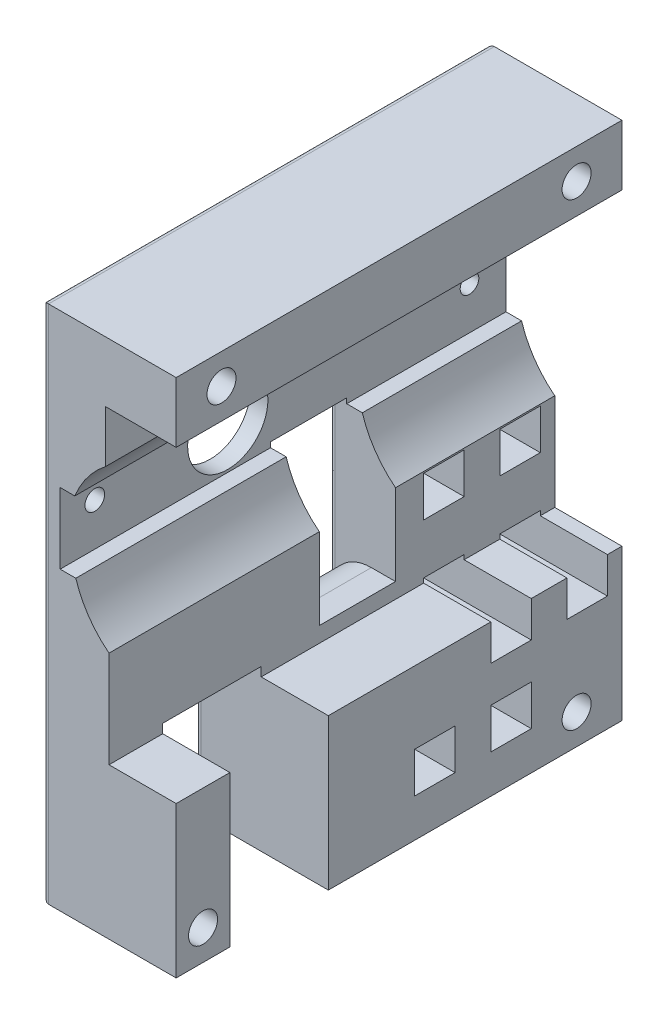
SolidWorks part; units mm, degrees
ref_plane "Front" through (0, 0, 0) normal (0, 0, 1) x (1, 0, 0)
ref_plane "Top" through (0, 0, 0) normal (0, 1, 0) x (1, 0, 0)
ref_plane "Right" through (0, 0, 0) normal (1, 0, 0) x (0, 0, -1)
sketch "Profile" plane through (0, 0, 0) normal (0, 0, 1) x (1, 0, 0)
  line L0 (10.2613, -54.1947) -> (10.2613, -29.1947)
  line L1 (-11.8487, -54.1947) -> (10.2613, -54.1947)
  line L2 (-11.8487, -54.1947) -> (-11.8487, 31.8453)
  line L3 (-11.8487, 31.8453) -> (10.2613, 31.8453)
  line L4 (10.2613, 21.8453) -> (10.2613, 31.8453)
  line L7 (10.2613, -29.1947) -> (-0.8487, -29.1947)
  line L8 (-0.8487, -29.1947) -> (-0.8487, -13.1947)
  line L10 (10.2613, 21.8453) -> (-1.3887, 21.8453)
  line L11 (-1.3887, 21.8453) -> (-1.3887, 13.2835)
  line L12 (-6.5097, 6.4953) -> (-8.9287, 6.4953)
  line L13 (-8.9287, 6.4953) -> (-8.9287, -5.2047)
  line L14 (-8.9287, -5.2047) -> (-6.3407, -5.2047)
  arc A0 (-6.3407, -5.2047) -> (-0.8487, -13.1947) centre (9.1965, -0.4075) ccw
  arc A1 (-6.5097, 6.4953) -> (-1.3887, 13.2835) centre (8.5807, 0.4371) cw
  point P0 (0, 0)
  dimension "D15" = 16.261
  dimension "D16" = 16.261
  dimension "D1" = 86.04
  dimension "D2" = 22.11
  dimension "D3" = 10
  dimension "D4" = 25
  dimension "D5" = 22.11
  dimension "D6" = 11.11
  dimension "D7" = 11.65
  dimension "D8" = 8.5617
  dimension "D9" = 16
  dimension "D10" = 2.588
  dimension "D11" = 11.7
  dimension "D12" = 2.4191
  dimension "D13" = 5.492
  dimension "D14" = 23.99
extrude "ProfileExtrude" add sketch "Profile" along normal blind 73.76
sketch "HoseWindow" plane through (-11.8487, 0, 0) normal (-1, 0, 0) x (0, 0, 1)
  line L0 (73.76, -54.1947) -> (0, -54.1947) construction
  line L1 (64.87, -54.1947) -> (48.58, -54.1947)
  line L2 (64.87, -54.1947) -> (64.87, -27.6947)
  line L3 (64.87, -27.6947) -> (48.58, -27.6947)
  line L4 (48.58, -54.1947) -> (48.58, -27.6947)
  dimension "D1" = 16.29
  dimension "D2" = 26.5
  dimension "D3" = 8.89
extrude "HoseWindowCut" cut sketch "HoseWindow" against normal through all
sketch "CageScrews" plane through (-11.8487, 0, 0) normal (-1, 0, 0) x (0, 0, 1)
  line L0 (73.76, 31.8453) -> (0, 31.8453) construction
  line L1 (0, 31.8453) -> (0, -54.1947) construction
  line L2 (73.76, 31.8453) -> (73.76, -54.1947) construction
  line L3 (73.76, -54.1947) -> (64.87, -54.1947) construction
  line L4 (48.58, -54.1947) -> (0, -54.1947) construction
  circle A0 centre (7.5, 26.8453) radius 2.4
  circle A1 centre (66.26, 26.8453) radius 2.4
  circle A2 centre (7.5, -49.1947) radius 2.4
  circle A3 centre (69.31, -49.1947) radius 2.4
  dimension "D1" = 4.8
  dimension "D2" = 5
  dimension "D3" = 7.5
  dimension "D4" = 7.5
  dimension "D5" = 5
  dimension "D6" = 5
  dimension "D7" = 4.45
  dimension "D8" = 5
  dimension "D9" = 7.5
extrude "CageScrewsCut" cut sketch "CageScrews" against normal through all
sketch "AxleHole" plane through (-11.8487, 0, 0) normal (-1, 0, 0) x (0, 0, 1)
  line L0 (46.03, -4.7837) -> (46.03, 6.7405) construction
  line L1 (47.361, 8.3595) -> (47.361, 6.7405)
  line L2 (47.361, 6.7405) -> (44.699, 6.7405)
  line L3 (44.699, 6.7405) -> (44.699, 8.3595)
  line L5 (48.58, -54.1947) -> (0, -54.1947) construction
  line L6 (0, 31.8453) -> (0, -54.1947) construction
  line L7 (39.391, 1.8553) -> (52.669, 1.8553) construction
  arc A0 (44.699, 8.3595) -> (47.361, 8.3595) centre (46.03, 1.8553) ccw
  dimension "D1" = 13.278
  dimension "D2" = 1.331
  dimension "D3" = 1.619
  dimension "D4" = 1.619
  dimension "D5" = 46.03
  dimension "D6" = 56.05
extrude "AxleHoleCut" cut sketch "AxleHole" against normal through all
sketch "SetScrewHoles" plane through (-11.8487, 0, 0) normal (-1, 0, 0) x (0, 0, 1)
  line L0 (47.361, 6.7405) -> (44.699, 6.7405) construction
  circle A0 centre (6.03, 1.8553) radius 1.5394
  circle A1 centre (68.03, 1.8553) radius 1.629
  point P6 (46.03, 6.7405)
  point P7 (46.03, 6.7405)
  dimension "D1" = 22
  dimension "D2" = 40
extrude "SetScrewHolesCut" cut sketch "SetScrewHoles" against normal through all
sketch "VelocityWindow" plane through (-11.8487, 0, 0) normal (-1, 0, 0) x (0, 0, 1)
  line L0 (73.76, 31.8453) -> (73.76, -54.1947) construction
  line L1 (38.96, -26.6447) -> (26.35, -26.6447)
  line L2 (38.96, -26.6447) -> (38.96, -4.3547)
  line L3 (38.96, -4.3547) -> (26.35, -4.3547)
  line L4 (26.35, -26.6447) -> (26.35, -4.3547)
  line L5 (38.96, -26.6447) -> (26.35, -4.3547) construction
  line L6 (38.96, -4.3547) -> (26.35, -26.6447) construction
  line L7 (48.58, -54.1947) -> (0, -54.1947) construction
  point P0 (32.655, -15.4997)
  dimension "D1" = 12.61
  dimension "D2" = 22.29
  dimension "D3" = 34.8
  dimension "D4" = 27.55
extrude "VelocityWindowCut" cut sketch "VelocityWindow" against normal through all
fillet "Fillet3" radius 7 1 edges at (-11.8487, -26.6447, 32.655)
sketch "TriggerRackSlotCut" plane through (-11.8487, 0, 0) normal (-1, 0, 0) x (0, 0, 1)
  line L0 (15, -41.1447) -> (21.7, -41.1447)
  line L1 (15, -41.1447) -> (15, -47.8447)
  line L2 (21.7, -41.1447) -> (21.7, -47.8447)
  line L3 (15, -47.8447) -> (21.7, -47.8447)
  line L4 (0, 31.8453) -> (0, -54.1947) construction
  line L5 (27.6, -41.1447) -> (34.3, -41.1447)
  line L6 (27.6, -41.1447) -> (27.6, -47.8447)
  line L7 (34.3, -41.1447) -> (34.3, -47.8447)
  line L8 (27.6, -47.8447) -> (34.3, -47.8447)
  line L9 (2.4, -28.4447) -> (9.1, -28.4447)
  line L10 (2.4, -28.4447) -> (2.4, -35.1447)
  line L11 (9.1, -28.4447) -> (9.1, -35.1447)
  line L12 (2.4, -35.1447) -> (9.1, -35.1447)
  line L13 (15, -28.4447) -> (21.7, -28.4447)
  line L14 (15, -28.4447) -> (15, -35.1447)
  line L15 (21.7, -28.4447) -> (21.7, -35.1447)
  line L16 (48.58, -54.1947) -> (0, -54.1947) construction
  line L17 (15, -35.1447) -> (21.7, -35.1447)
  line L18 (15, -41.1447) -> (27.6, -41.1447) construction
  line L19 (15, -41.1447) -> (15, -28.4447) construction
  line L20 (2.4, -13.4447) -> (9.1, -13.4447)
  line L21 (2.4, -13.4447) -> (2.4, -20.1447)
  line L22 (9.1, -13.4447) -> (9.1, -20.1447)
  line L23 (2.4, -20.1447) -> (9.1, -20.1447)
  line L24 (15, -13.4447) -> (21.7, -13.4447)
  line L25 (15, -13.4447) -> (15, -20.1447)
  line L26 (21.7, -13.4447) -> (21.7, -20.1447)
  line L27 (15, -20.1447) -> (21.7, -20.1447)
  line L28 (15, -28.4447) -> (2.4, -28.4447) construction
  line L43 (27.6, -28.4447) -> (34.3, -28.4447) [skipped]
  line L44 (27.6, -28.4447) -> (27.6, -35.1447) [skipped]
  line L45 (34.3, -28.4447) -> (34.3, -35.1447) [skipped]
  line L46 (27.6, -35.1447) -> (34.3, -35.1447) [skipped]
  dimension "D1" = 6.35
  dimension "D2" = 15
  dimension "D3" = 6.7
  dimension "D4" = 6.7
  dimension "D7" = 2
  dimension "D5" = 12.6
  dimension "D6" = 12.7
  dimension "D9" = 12.6
  dimension "D8" = 2
extrude "RackSlotCut" cut sketch "TriggerRackSlotCut" against normal through all
fillet "Fillet4" radius 1 35 edges at (-11.8487, -31.7947, 21.7) (-11.8487, -28.4447, 18.35) (-11.8487, -31.7947, 15) (-11.8487, -35.1447, 18.35) (-11.8487, -47.8447, 18.35) (-11.8487, -44.4947, 15) (-11.8487, -41.1447, 18.35) (-11.8487, -44.4947, 21.7) (-11.8487, -47.8447, 30.95) (-11.8487, -44.4947, 34.3) (-11.8487, -18.9997, 38.96) (-11.8487, -4.3547, 32.655) (-11.8487, -18.9997, 26.35) (-11.8487, -11.1747, 0) (-11.8487, -54.1947, 24.29) (-11.8487, -40.9447, 48.58) (-11.8487, -27.6947, 56.725) (-11.8487, -40.9447, 64.87) (-11.8487, -54.1947, 69.315) (-11.8487, -11.1747, 73.76) (-11.8487, 31.8453, 36.88) (-11.8487, -44.4947, 27.6) (-11.8487, -41.1447, 30.95) (-11.8487, -35.1447, 5.75) (-11.8487, -31.7947, 2.4) (-11.8487, -31.7947, 9.1) (-11.8487, -28.4447, 5.75) (-11.8487, -13.4447, 18.35) (-11.8487, -16.7947, 21.7) (-11.8487, -20.1447, 18.35) (-11.8487, -16.7947, 15) (-11.8487, -16.7947, 2.4) (-11.8487, -20.1447, 5.75) (-11.8487, -16.7947, 9.1) (-11.8487, -13.4447, 5.75)
equation "\"CageLeftBottomEdge\"=22.11mm"
equation "\"CageLeftTopEdge\"=22.11mm"
equation "\"CageHeight\"=86.04mm"
equation "\"CageLength\"=73.76mm"
equation "\"CageTopScrewClearance\"=10mm"
equation "\"CageLeftTopDepth\"= 11.65mm"
equation "\"CageLeftBottomDepth\"=11.11mm"
equation "\"CageLeftTopHeight\"=8.56175mm"
equation "\"CageLeftBottomHeight\"=16mm"
equation "\"CageLeftTopChannelDepth\"=2.41908mm"
equation "\"CageLeftBottomChannelDepth\"=2.588mm"
equation "\"CageLeftChannelHeight\"=11.7mm"
equation "\"CageChanRelHeight\"=23.99mm"
equation "\"CageChanRelDepth\"=5.492mm"
equation "\"CageChamberRadius\"=16.261mm"
equation "\"CageScrewDiameter\"=4.8mm"
equation "\"CageSetScrewDiameter\"=3.5mm"
equation "\"CageAxleRadius\"=6.639mm"
equation "\"CageAxleKeyHeight\"=1.619mm"
equation "\"CageAxleKeyWidth\"=2.662mm"
equation "\"CageHoseWindowWidth\"=16.29mm"
equation "\"CageHoseWindowHeight\"=26.5mm"
equation "\"CageHoseWindow-Edge\"=8.89mm"
equation "\"CageScrew-VerticalEdge\"=5.0mm"
equation "\"CageScrew-HorizontalEdge\"=7.5mm"
equation "\"CageScrew-HoseCornerScrewEdge\"=4.45mm"
equation "\"CageAxle-BottomEdge\"=56.05mm"
equation "\"CageBackSetScrew-Axle\"=40mm"
equation "\"CageFrontSetScrew-Axle\"=22mm"
equation "\"CageVelocityWindow-BackEdge\"=34.8mm"
equation "\"CageVelocityWindow-BottomEdge\"=27.55mm"
equation "\"CageVelocityWindowHeight\"=22.29mm"
equation "\"CageVelocityWindowWidth\"=12.61mm"
equation "\"D11@Profile\" = \"CageLeftChannelHeight\""
equation "\"D10@Profile\" = \"CageLeftBottomChannelDepth\""
equation "\"D12@Profile\" = \"CageLeftTopChannelDepth\""
equation "\"D8@Profile\" = \"CageLeftTopHeight\""
equation "\"D9@Profile\" = \"CageLeftBottomHeight\""
equation "\"D6@Profile\" = \"CageLeftBottomDepth\""
equation "\"D7@Profile\" = \"CageLeftTopDepth\""
equation "\"D3@Profile\" = \"CageTopScrewClearance\""
equation "\"CageBottomScrewClearance\"=25mm"
equation "\"D4@Profile\" = \"CageBottomScrewClearance\""
equation "\"D5@Profile\" = \"CageLeftBottomEdge\""
equation "\"D2@Profile\" = \"CageLeftTopEdge\""
equation "\"D1@Profile\" = \"CageHeight\""
equation "\"D13@Profile\" = \"CageChanRelDepth\""
equation "\"D14@Profile\" = \"CageChanRelHeight\""
equation "\"D15@Profile\" = \"CageChamberRadius\""
equation "\"D16@Profile\" = \"CageChamberRadius\""
equation "\"D1@ProfileExtrude\"= \"CageLength\""
equation "\"D3@HoseWindow\" = \"CageHoseWindow-Edge\""
equation "\"D2@HoseWindow\" = \"CageHoseWindowHeight\""
equation "\"D1@HoseWindow\" = \"CageHoseWindowWidth\""
equation "\"D1@CageScrews\"= \"CageScrewDiameter\""
equation "\"D9@CageScrews\" = \"CageScrew-HorizontalEdge\""
equation "\"D7@CageScrews\" = \"CageScrew-HoseCornerScrewEdge\""
equation "\"D4@CageScrews\" = \"CageScrew-HorizontalEdge\""
equation "\"D6@CageScrews\"= \"CageScrew-VerticalEdge\""
equation "\"D5@CageScrews\"= \"CageScrew-VerticalEdge\""
equation "\"D8@CageScrews\"= \"CageScrew-VerticalEdge\""
equation "\"D2@CageScrews\"= \"CageScrew-VerticalEdge\""
equation "\"D1@AxleHole\" = \"CageAxleRadius\" * 2"
equation "\"D4@AxleHole\" = \"CageAxleKeyHeight\""
equation "\"D3@AxleHole\" = \"CageAxleKeyHeight\""
equation "\"D2@AxleHole\" = \"CageAxleKeyWidth\" / 2"
equation "\"CageAxle-FrontEdge\"=46.03mm"
equation "\"D6@AxleHole\" = \"CageAxle-BottomEdge\""
equation "\"D5@AxleHole\" = \"CageAxle-FrontEdge\""
equation "\"D2@SetScrewHoles\" = \"CageBackSetScrew-Axle\""
equation "\"D1@SetScrewHoles\" = \"CageFrontSetScrew-Axle\""
equation "\"D1@VelocityWindow\" = \"CageVelocityWindowWidth\""
equation "\"D2@VelocityWindow\" = \"CageVelocityWindowHeight\""
equation "\"D3@VelocityWindow\" = \"CageVelocityWindow-BackEdge\""
equation "\"D4@VelocityWindow\"= \"CageVelocityWindow-BottomEdge\""
equation "\"TriggerSlot-BottomEdge\"=6.35mm"
equation "\"D1@TriggerRackSlotCut\" = \"TriggerSlot-BottomEdge\""
equation "\"TriggerSlot-FrontEdge\"=15mm"
equation "\"TriggerSlotSize\"=6.7mm"
equation "\"D3@TriggerRackSlotCut\" = \"TriggerSlotSize\""
equation "\"D4@TriggerRackSlotCut\" = \"TriggerSlotSize\""
equation "\"D2@TriggerRackSlotCut\" = \"TriggerSlot-FrontEdge\""
equation "\"CageRightBottomEdge\"=21.63mm"
equation "\"CageRightTopEdge\"=21.63mm"
equation "\"CageRightTopDepth\"= 11.05mm"
equation "\"CageRightBottomDepth\"=10.58mm"
equation "\"CageRightTopHeight\"=9.6mm"
equation "\"CageRightBottomHeight\"=15.49mm"
equation "\"CageRightTopChannelDepth\"=2.32mm"
equation "\"CageRightBottomChannelDepth\"=2.318mm"
equation "\"CageRightChannelHeight\"=10mm"
equation "\"vigorwidth\"= 0.472441in"
equation "\"vigorflangewidth\"= 0.731102in"
equation "\"vigorflangelength\"= 0.131102in"
equation "\"vigorscrewsize\"= 0.066535in"
equation "\"vigorholeoffsetwid\"= 0.0646653in"
equation "\"vigorholeoffsetlen\"= 0.065551in"
equation "\"vigorflangedepth\"= 0.0901575in"
equation "\"vigordiscdepth\"= 0.0492126in"
equation "\"vigormotordepth\"= 1.12362in"
equation "\"vigortipdepth\"= 0.259055in"
equation "\"vigoraxlewidth\"= 0.173622in"
equation "\"vigorcutlen\"= 0.0480315in"
equation "\"vigoraxledepth\"= 0.159055in"
equation "\"TriggerRackOffset\"=.236224in"
equation "\"TriggerSlotSizeInt\"=.25in"
equation "\"MotorMountLegLength\"=.25in"
equation "\"GearOffset\"=.264907in"
equation "\"TriggerSlotSpacing\"=.25in"
equation "\"TriggerMiniSlotWidth\"=3.5mm"
equation "\"TriggerRackWidth\"=6.5mm"
equation "\"TGMGearFaceDiameter\"=24.40mm"
equation "\"TGMCylinderLength\"=15.00mm"
equation "\"TGMScrewHole-Center\"=8.70mm"
equation "\"TGMScrewHoleDiameter\"=5.04mm"
equation "\"TGMCenterHoleDiameter\"=9.50mm"
equation "\"TGMShaftCollarSideLength\"=19.00mm"
equation "\"TGMShaftCollarDockingDepth\"=7.00mm"
equation "\"whitemotordepth\"=11.27mm"
equation "\"whitemotorbackdepth\"=3.845mm"
equation "\"whitemotoraxledepth\" = 3.5mm"
equation "\"whitemotoraxleoffset\"=11.4mm"
equation "\"whitemotorwidth\"=12.07mm"
equation "\"whitemotorheight\"=16.68mm"
equation "\"whitemotorcylinderlength\" =13.04mm"
equation "\"whitemotorcylinderradius\"=3.845mm"
equation "\"whitemotorcylinderoffset\"=2.35mm"
equation "\"whitemotorcutoutlength\"=1.88mm"
equation "\"whitemotorouterrad\"=5mm"
